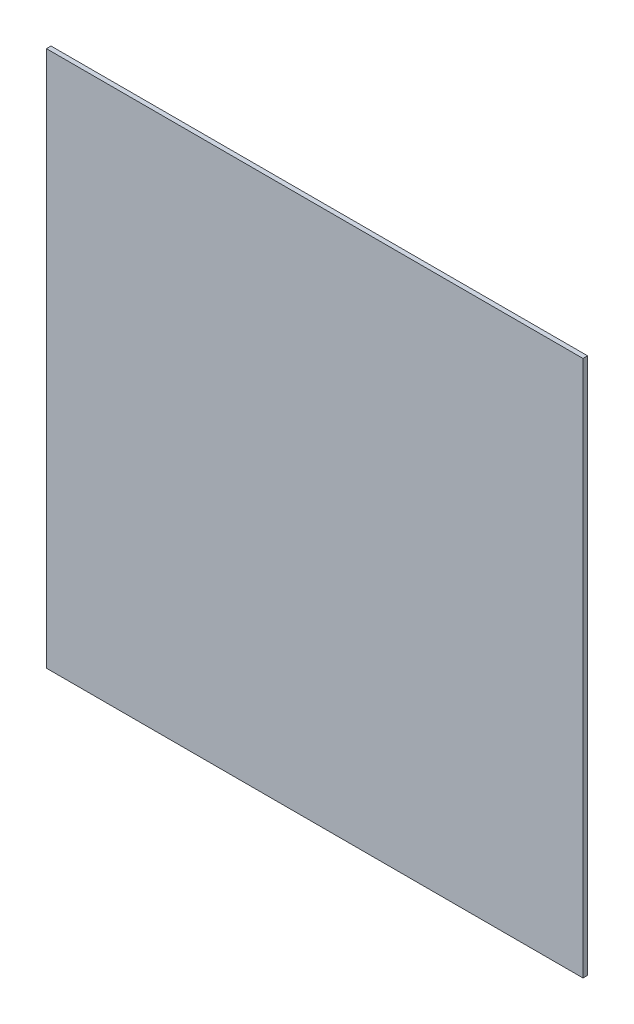
SolidWorks part; units mm, degrees
ref_plane "Front Plane" through (0, 0, 0) normal (0, 0, 1) x (1, 0, 0)
ref_plane "Top Plane" through (0, 0, 0) normal (0, 1, 0) x (1, 0, 0)
ref_plane "Right Plane" through (0, 0, 0) normal (1, 0, 0) x (0, 0, -1)
sketch "Sketch1" plane through (0, 0, 0) normal (0, 0, 1) x (1, 0, 0)
  line L1 (-585, 585) -> (585, 585)
  line L2 (-585, 585) -> (-585, -585)
  line L3 (-585, -585) -> (585, -585)
  line L4 (585, 585) -> (585, -585)
  line L5 (-585, 585) -> (585, -585) construction
  line L6 (-585, -585) -> (585, 585) construction
  point P0 (0, 0)
  dimension "D1" = 1170
  dimension "D2" = 1170
extrude "Boss-Extrude1" add sketch "Sketch1" along normal mid plane 10
